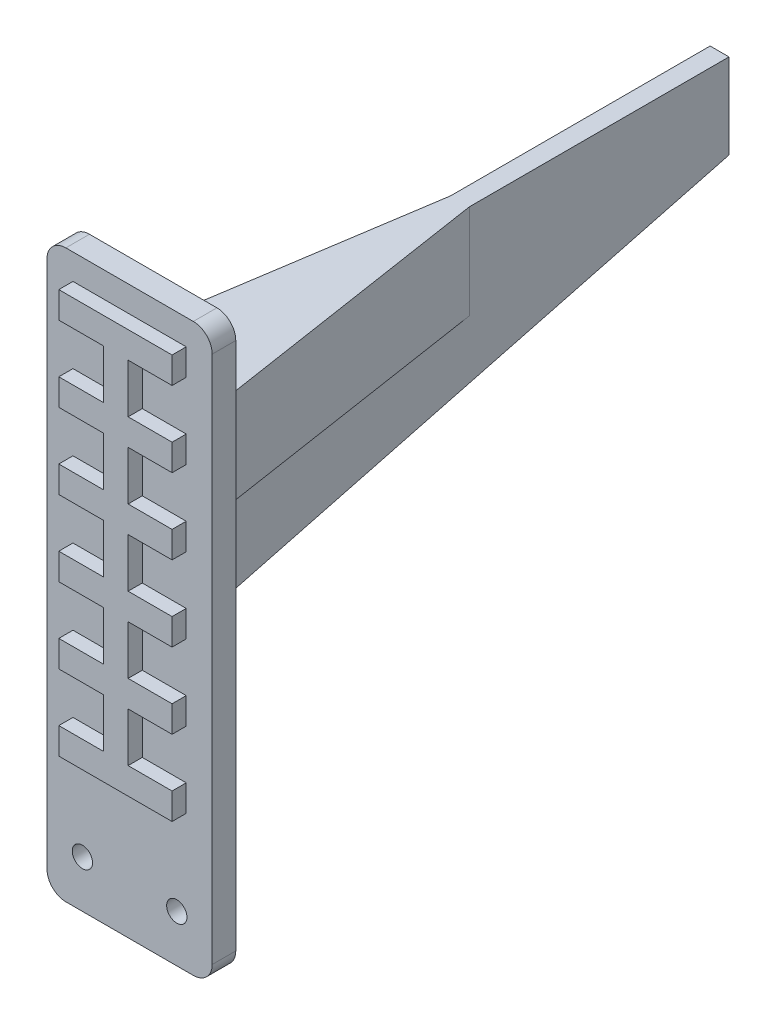
SolidWorks part; units mm, degrees
ref_plane "前视基准面" through (0, 0, 0) normal (0, 0, 1) x (1, 0, 0)
ref_plane "上视基准面" through (0, 0, 0) normal (0, 1, 0) x (1, 0, 0)
ref_plane "右视基准面" through (0, 0, 0) normal (1, 0, 0) x (0, 0, -1)
other "Configuration Table"
sketch "Sketch1" plane through (0, 0, 0) normal (0, 0, 1) x (1, 0, 0)
  line L1 (0, 0) -> (35, 0)
  line L2 (0, 0) -> (0, -20)
  line L3 (0, -20) -> (35, -20)
  line L4 (35, 0) -> (35, -20)
  line L5 (10, 0) -> (25, 0)
  line L6 (10, 0) -> (10, 100)
  line L7 (10, 100) -> (25, 100)
  line L8 (25, 0) -> (25, 100)
  dimension "D1" = 20
  dimension "D2" = 35
  dimension "D3" = 15
  dimension "D4" = 100
  dimension "D5" = 10
extrude "Boss-Extrude1" add sketch "Sketch1" along normal blind 5 contours L1 L8 L7 L6 | L4 L1 L2 L3
sketch "Sketch2" plane through (0, 0, 5) normal (0, 0, 1) x (1, 0, 0)
  line L0 (10, 0) -> (10, 100) construction
  line L1 (15, 93) -> (20, 93)
  line L2 (15, 93) -> (15, -3)
  line L3 (15, -17) -> (20, -17)
  line L4 (20, 93) -> (20, -3)
  line L5 (5, -3) -> (15, -3)
  line L6 (5, -3) -> (5, -6.5)
  line L7 (5, -6.5) -> (15, -6.5)
  line L8 (32, -3) -> (32, -6.5)
  line L9 (4.9371, -10.1413) -> (15, -10.1413)
  line L10 (4.9371, -10.1413) -> (4.9371, -13.3373)
  line L11 (4.9371, -13.3373) -> (15, -13.3373)
  line L12 (31.0217, -10.1413) -> (31.0217, -13.3373)
  line L13 (0, 0) -> (10, 0) construction
  line L14 (0, -20) -> (35, -20) construction
  line L15 (0, 0) -> (0, -20) construction
  line L16 (20, -3) -> (32, -3)
  line L17 (15, -6.5) -> (15, -10.1413)
  line L18 (20, -6.5) -> (20, -10.1413)
  line L19 (20, -6.5) -> (32, -6.5)
  line L20 (20, -10.1413) -> (31.0217, -10.1413)
  line L21 (15, -13.3373) -> (15, -17)
  line L22 (20, -13.3373) -> (20, -17)
  line L23 (20, -13.3373) -> (31.0217, -13.3373)
  dimension "D1" = 110
  dimension "D2" = 5
  dimension "D3" = 5
  dimension "D4" = 3
  dimension "D5" = 3.5
  dimension "D6" = 5
  dimension "D7" = 27
  dimension "D8" = 3
  dimension "D9" = 4.9371
  dimension "D10" = 31.0217
  dimension "D11" = 6.6627
  dimension "D12" = 9.8587
sketch "Sketch3" plane through (0, 0, 0) normal (0, 0, -1) x (-1, 0, 0)
  line L0 (-17.5, -20) -> (-17.5, 100) construction
  line L1 (0, -20) -> (-35, -20) construction
  line L2 (-10, 100) -> (-25, 100) construction
  circle A0 centre (-27.5, -10) radius 2.15
  circle A2 centre (-7.5, -10) radius 2.15
  dimension "D1" = 4.3
  dimension "D2" = 20
  dimension "D3" = 10
extrude "Cut-Extrude1" cut sketch "Sketch3" against normal through all
sketch "Sketch4" plane through (0, 0, 0) normal (0, 0, -1) x (-1, 0, 0)
  line L0 (-35, 0) -> (-25, 0)
  line L1 (-25, 0) -> (-25, 62)
  line L2 (-25, 0) -> (-25, 100) construction
  line L3 (-25, 62) -> (-35, 0)
  line L4 (-17.5, 100) -> (-17.5, 0) construction
  line L5 (-10, 100) -> (-25, 100) construction
  line L6 (-10, 62) -> (0, 0)
  line L7 (0, 0) -> (-10, 0)
  line L8 (-10, 0) -> (-10, 62)
  point P14 (0, 0)
  dimension "D1" = 62
extrude "Boss-Extrude3" add sketch "Sketch4" against normal up to surface (5 mm away) up to face at (25.35, -10, 5)
ref_plane "Plane1" through (17.5, 0, 0) normal (-1, 0, 0) x (0, 0, 1)
sketch "Sketch5" plane through (17.5, 0, 0) normal (-1, 0, 0) x (0, 0, 1)
  line L0 (0, 80.2915) -> (0, 31)
  line L1 (0, 62) -> (0, 100) construction
  line L2 (0, 0) -> (0, 62) construction
  line L3 (0, 31) -> (-120, 62.2915)
  line L4 (-120, 62.2915) -> (-120, 80.2915)
  line L5 (-120, 80.2915) -> (0, 80.2915)
  dimension "D1" = 120
  dimension "D2" = 18
  dimension "D3" = 62.2915
extrude "Boss-Extrude4" add sketch "Sketch5" along normal mid plane 4
sketch "Sketch6" plane through (0, 0, 5) normal (0, 0, 1) x (1, 0, 0)
  line L0 (25, 62) -> (35, 0) construction
  line L1 (25, 62) -> (25, 100) construction
  line L2 (10, 100) -> (25, 100) construction
  line L3 (10, 62) -> (10, 100) construction
  line L4 (0, 0) -> (10, 62) construction
  line L5 (25, 62) -> (35, 0)
  line L6 (25, 62) -> (25, 100)
  line L7 (10, 100) -> (25, 100)
  line L8 (10, 62) -> (10, 100)
  line L9 (0, 0) -> (10, 62)
  line L10 (10, 100) -> (0, 100)
  line L11 (0, 100) -> (0, 0)
  line L12 (25, 100) -> (35, 100)
  line L13 (35, 100) -> (35, 0)
extrude "Boss-Extrude5" add sketch "Sketch6" against normal up to surface (5 mm away) contours L13 L12 L6 L5 | L10 L11 L9 L8 up to face at (9.65, -10, 0)
sketch "Sketch7" plane through (0, 80.2915, 0) normal (0, 1, 0) x (1, 0, 0)
  line L0 (15.5, 65) -> (15.5, 0)
  line L1 (15.5, 0) -> (15.5, 120) construction
  line L2 (15.5, 0) -> (5.5, 0)
  line L3 (0, 0) -> (35, 0) construction
  line L4 (5.5, 0) -> (15.5, 65)
  line L5 (17.5, 0) -> (17.5, 120) construction
  line L6 (15.5, 0) -> (19.5, 0) construction
  line L7 (15.5, 120) -> (19.5, 120) construction
  line L8 (19.5, 0) -> (29.5, 0)
  line L9 (19.5, 65) -> (19.5, 0)
  line L10 (29.5, 0) -> (19.5, 65)
  point P5 (5.5, 0)
  point P15 (15.5, 76.5216)
  point P16 (0, 0)
  dimension "D1" = 10
  dimension "D2" = 65
extrude "Boss-Extrude6" add sketch "Sketch7" against normal blind 20
fillet "Fillet3" radius 4 4 edges at (35, 100, 2.5) (35, -20, 2.5) (0, 100, 2.5) (0, -20, 2.5)
sketch "Sketch8" plane through (0, 0, 5) normal (0, 0, 1) x (1, 0, 0)
  line L0 (17.5, 100) -> (17.5, -20) construction
  line L1 (5.5, 14.5955) -> (29.5, 14.5955)
  line L2 (5.5, 14.5955) -> (5.5, 8.9921)
  line L3 (5.5, 8.9921) -> (29.5, 8.9921)
  line L4 (29.5, 14.5955) -> (29.5, 8.9921)
  line L5 (4, 100) -> (31, 100) construction
  line L6 (4, -20) -> (31, -20) construction
  line L9 (5.5, 30.5955) -> (5.5, 24.9921)
  line L10 (5.5, 30.5955) -> (29.5, 30.5955)
  line L11 (29.5, 30.5955) -> (29.5, 24.9921)
  line L12 (5.5, 24.9921) -> (29.5, 24.9921)
  line L13 (5.5, 46.5955) -> (5.5, 40.9921)
  line L14 (5.5, 46.5955) -> (29.5, 46.5955)
  line L15 (29.5, 46.5955) -> (29.5, 40.9921)
  line L16 (5.5, 40.9921) -> (29.5, 40.9921)
  line L17 (5.5, 62.5955) -> (5.5, 56.9921)
  line L18 (5.5, 62.5955) -> (29.5, 62.5955)
  line L19 (29.5, 62.5955) -> (29.5, 56.9921)
  line L20 (5.5, 56.9921) -> (29.5, 56.9921)
  line L21 (5.5, 78.5955) -> (5.5, 72.9921)
  line L22 (5.5, 78.5955) -> (29.5, 78.5955)
  line L23 (29.5, 78.5955) -> (29.5, 72.9921)
  line L24 (5.5, 72.9921) -> (29.5, 72.9921)
  line L25 (5.5, 94.5955) -> (5.5, 88.9921)
  line L26 (5.5, 94.5955) -> (29.5, 94.5955)
  line L27 (29.5, 94.5955) -> (29.5, 88.9921)
  line L28 (5.5, 88.9921) -> (29.5, 88.9921)
  line L29 (35, 96) -> (35, -16) construction
  line L30 (14.98, 8.9921) -> (20.1847, 8.9921)
  line L31 (14.98, 8.9921) -> (14.98, 94.5955)
  line L32 (14.98, 94.5955) -> (20.1847, 94.5955)
  line L33 (20.1847, 8.9921) -> (20.1847, 94.5955)
  dimension "D1" = 12
  dimension "D2" = 24
  dimension "D3" = 85.4045
  dimension "D4" = 91.0079
  dimension "D5" = 6
  dimension "D6" = 14.8153
  dimension "D7" = 20.02
  dimension "D8" = 5.4045
extrude "Boss-Extrude7" add sketch "Sketch8" along normal blind 3 contours L28 L31 L26 L25 | L32 L0 L28 L33 | L0 L26 L31 L28 | L33 L28 L27 L26 | L28 L0 L22 L33 | L0 L28 L31 L22 | L24 L31 L22 L21 | L0 L22 L31 L24 | L22 L0 L24 L33 | L33 L24 L23 L22 | L24 L0 L18 L33 | L0 L24 L31 L18 | L20 L31 L18 L17 | L0 L18 L31 L20 | L18 L0 L20 L33 | L33 L20 L19 L18 | L33 L16 L15 L14 | L16 L31 L14 L13 | L12 L31 L10 L9 | L33 L12 L11 L10 | L33 L3 L4 L1 | L3 L31 L1 L2
